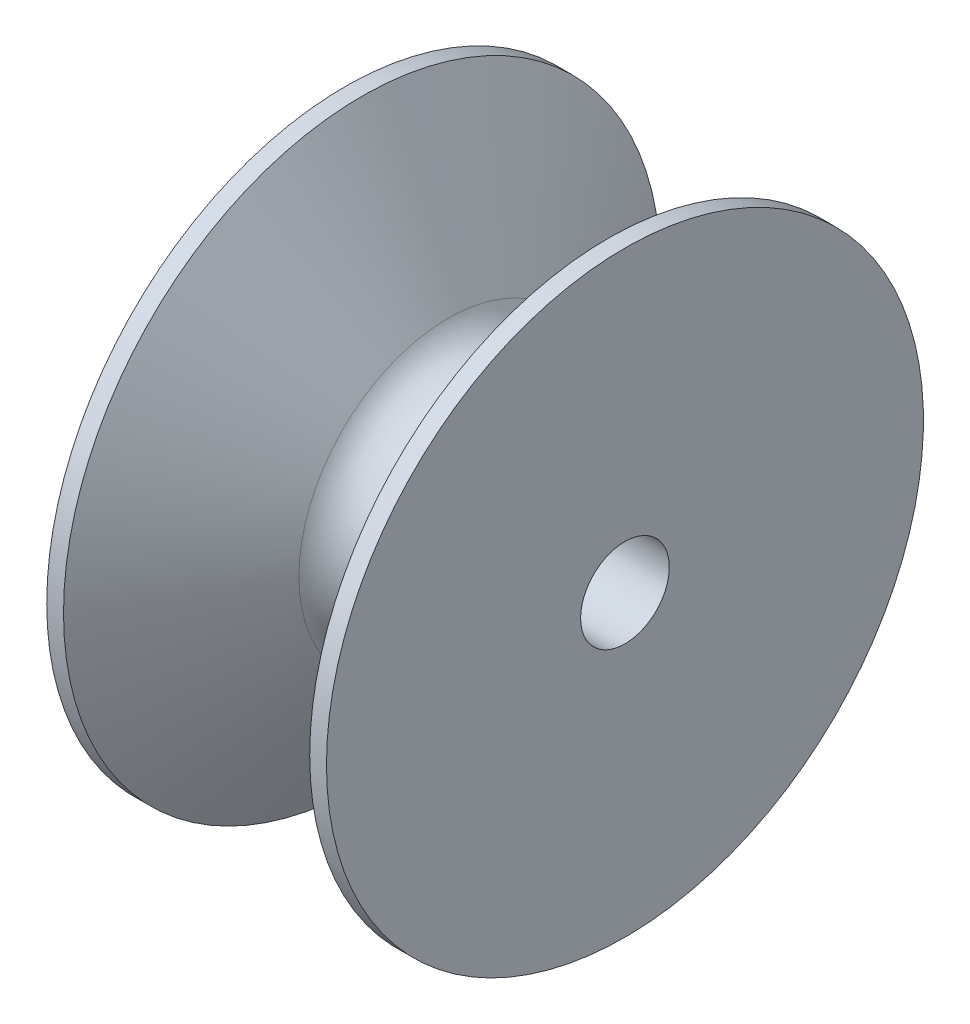
SolidWorks part; units mm, degrees
material "PET"
ref_plane "Front" through (0, 0, 0) normal (0, 0, 1) x (1, 0, 0)
ref_plane "Top" through (0, 0, 0) normal (0, 1, 0) x (1, 0, 0)
ref_plane "Right" through (0, 0, 0) normal (1, 0, 0) x (0, 0, -1)
sketch "Sketch1" plane through (0, 0, 0) normal (0, 0, 1) x (1, 0, 0)
  line L0 (0, 1.651) -> (10.414, 1.651)
  line L1 (10.414, 1.651) -> (10.414, 11.1125)
  line L2 (10.414, 11.1125) -> (9.7897, 11.1125)
  line L3 (9.7897, 11.1125) -> (6.5818, 5.5563)
  line L4 (3.8322, 5.5563) -> (0.6243, 11.1125)
  line L5 (0.6243, 11.1125) -> (0, 11.1125)
  line L6 (0, 11.1125) -> (0, 1.651)
  line L7 (0, 0) -> (13.0175, 0) construction
  arc A0 (6.5818, 5.5563) -> (3.8322, 5.5563) centre (5.207, 6.35) cw
  dimension "D4" = 9.525
  dimension "D6" = 3.175
  dimension "D1" = 10.414
  dimension "D2" = 3.302
  dimension "D3" = 22.225
  dimension "D5" = 60
revolve "Revolve1" add sketch "Sketch1" angle 360 about L7
